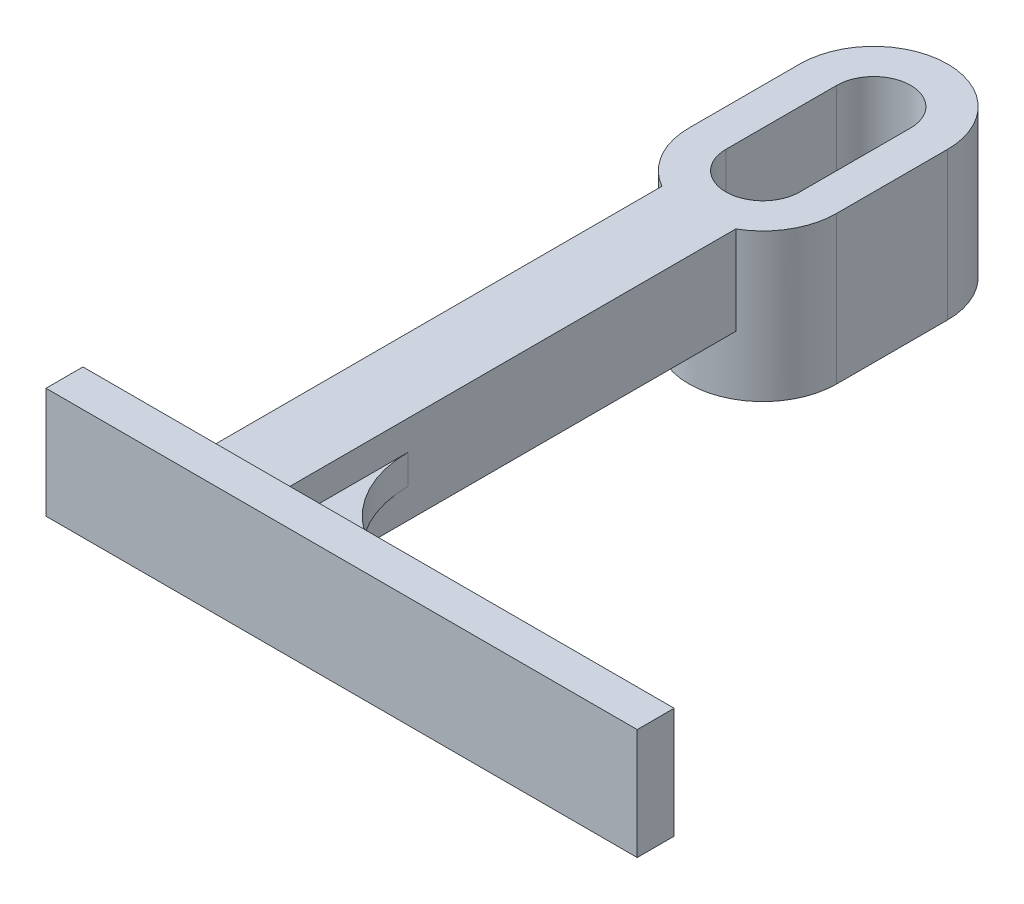
SolidWorks part; units mm, degrees
ref_plane "Front Plane" through (0, 0, 0) normal (0, 0, 1) x (1, 0, 0)
ref_plane "Top Plane" through (0, 0, 0) normal (0, 1, 0) x (1, 0, 0)
ref_plane "Right Plane" through (0, 0, 0) normal (1, 0, 0) x (0, 0, -1)
sketch "Sketch1" plane through (0, 0, 0) normal (0, 1, 0) x (1, 0, 0)
  line L0 (0, 0) -> (0, -15) construction
  line L1 (5, 0) -> (5, -15)
  line L2 (-5, 0) -> (-5, -15)
  line L3 (0, 0) -> (0, -15) construction
  line L4 (10, 0) -> (10, -15)
  line L5 (-10, 0) -> (-10, -15)
  line L6 (0, -20) -> (0, -92) construction
  line L7 (-5, -23.6603) -> (-5, -92)
  line L8 (5, -23.6603) -> (5, -92)
  line L10 (0, -17.2847) -> (0, -92) construction
  line L11 (5, -17.2847) -> (5, -92) construction
  line L12 (-5, -17.2847) -> (-5, -92) construction
  line L13 (-20, -92) -> (60, -92)
  line L14 (-20, -92) -> (-20, -87)
  line L15 (-20, -87) -> (60, -87)
  line L16 (60, -92) -> (60, -87)
  arc A0 (5, 0) -> (-5, 0) centre (0, 0) ccw
  arc A1 (-5, -15) -> (5, -15) centre (0, -15) ccw
  arc A2 (10, 0) -> (-10, 0) centre (0, 0) ccw
  arc A3 (-10, -15) -> (-5, -23.6603) centre (0, -15) ccw
  arc A4 (5, -23.6603) -> (10, -15) centre (0, -15) ccw
  point P3 (0, -7.5)
  point P10 (0, -7.5)
  point P24 (-20, -89.5)
  dimension "D2" = 5
  dimension "D3" = 10
  dimension "D1" = 15
  dimension "D4" = 15
  dimension "D7" = 80
  dimension "D8" = 5
  dimension "D9" = 72
  dimension "D5" = 5
  dimension "D6" = 5
extrude "Boss-Extrude1" add sketch "Sketch1" along normal blind 12 contours L8 A4 L4 A2 L5 A3 L7 L15 A1 L2 A0 L1
sketch "Sketch2" plane through (0, 0, 0) normal (0, -1, 0) x (1, 0, 0)
  line L0 (5, 0) -> (5, 15) construction
  line L1 (-5, 0) -> (-5, 15) construction
  line L2 (-5, 0) -> (-5, 15)
  line L3 (5, 0) -> (5, 15)
  line L4 (0, 15) -> (0, 0) construction
  line L5 (10, 15) -> (10, 0)
  line L6 (-10, 15) -> (-10, 0)
  arc A0 (-5, 0) -> (5, 0) centre (0, 0) ccw construction
  arc A1 (5, 15) -> (-5, 15) centre (0, 15) ccw construction
  arc A2 (-5, 0) -> (5, 0) centre (0, 0) ccw
  arc A3 (5, 15) -> (-5, 15) centre (0, 15) ccw
  arc A4 (10, 15) -> (-10, 15) centre (0, 15) ccw
  arc A5 (-10, 0) -> (10, 0) centre (0, 0) ccw
  point P0 (0, 7.5)
  dimension "D1" = 10
extrude "Boss-Extrude2" add sketch "Sketch2" along normal blind 8
sketch "Sketch3" plane through (0, 12, 0) normal (0, 1, 0) x (1, 0, 0)
  line L1 (-20, -87) -> (60, -87)
  line L2 (-20, -87) -> (-20, -92)
  line L3 (-20, -92) -> (60, -92)
  line L4 (60, -87) -> (60, -92)
extrude "Boss-Extrude3" add sketch "Sketch3" along normal blind 3
ref_plane "Plane1" through (0, 6, 0) normal (0, 1, 0) x (1, 0, 0)
sketch "Sketch4" plane through (0, 6, 0) normal (0, 1, 0) x (1, 0, 0)
  line L0 (-20, -87) -> (-5, -87) construction
  line L1 (-5, -23.6603) -> (-5, -87) construction
  line L2 (-5, -72) -> (-20, -72) construction
  line L3 (-20, -72) -> (-20, -87) construction
  line L4 (5, -23.6603) -> (5, -87) construction
  line L5 (5, -87) -> (60, -87) construction
  line L6 (16.018, -82.4618) -> (32.5, -87)
  line L7 (32.5, -87) -> (5, -87)
  line L8 (5, -87) -> (5, -68)
  line L9 (-5, -72) -> (-5, -87)
  line L10 (-5, -87) -> (-20, -87)
  arc A0 (-20, -87) -> (-5, -72) centre (-20, -72) ccw
  arc A1 (5, -68) -> (16.018, -82.4618) centre (20, -68) ccw
  dimension "D1" = 15
  dimension "D3" = 30
  dimension "D4" = 19
extrude "Boss-Extrude4" add sketch "Sketch4" along normal mid plane 4
